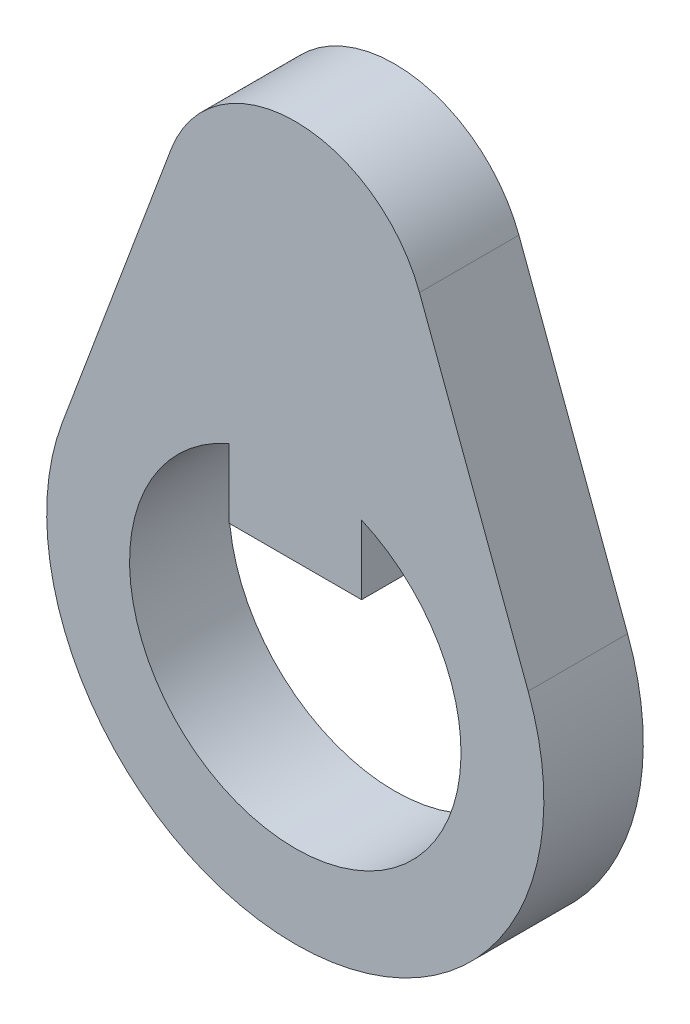
SolidWorks part; units mm, degrees
ref_plane "Front Plane" through (0, 0, 0) normal (0, 0, 1) x (1, 0, 0)
ref_plane "Top Plane" through (0, 0, 0) normal (0, 1, 0) x (1, 0, 0)
ref_plane "Right Plane" through (0, 0, 0) normal (1, 0, 0) x (0, 0, -1)
sketch "Sketch1" plane through (0, 0, 0) normal (0, 0, 1) x (1, 0, 0)
  line L0 (4, 15) -> (-4, 15)
  line L1 (4, 15) -> (4, 5)
  line L2 (4, 5) -> (-4, 5)
  line L3 (-4, 15) -> (-4, 5)
  line L4 (4, 15) -> (-4, 5) construction
  line L5 (4, 5) -> (-4, 15) construction
  line L6 (-7.494, 22.8) -> (-14.0512, 5.25)
  line L7 (7.494, 22.8) -> (14.0512, 5.25)
  circle A1 centre (0, 0) radius 10
  arc A2 (-7.494, 22.8) -> (7.494, 22.8) centre (0, 20) cw
  arc A3 (-14.0512, 5.25) -> (14.0512, 5.25) centre (0, 0) ccw
  point P3 (0, 10)
  dimension "D4" = 20
  dimension "D5" = 15
  dimension "D6" = 8
  dimension "D1" = 20
  dimension "D2" = 8
  dimension "D3" = 10
extrude "Boss-Extrude1" add sketch "Sketch1" along normal blind 6 contours L6 A3 L7 A2 A1 L3 L0 L1 | A1 L1 L0 L3 | L1 A1 L3 L2
equation "\"shaftDiam\" = 20mm"
equation "\"keyW\" = 8mm"
equation "\"keyL\" = 10mm"
equation "\"clearance\" = 1mm"
equation "\"handleShaftLen\" = 60mm"
equation "\"panelH\" = 80mm"
equation "\"panelW\" = 110mm"
equation "\"D2@Sketch1\"=\"keyW\""
equation "\"D3@Sketch1\"=\"keyL\""
equation "\"D4@Sketch1\"=\"shaftDiam\""
equation "\"D5@Sketch1\"=\"shaftDiam\"*.75"
equation "\"D1@Sketch1\"=\"shaftDiam\""
equation "\"D6@Sketch1\"=\"shaftDiam\"/2.5"
equation "\"D1@Boss-Extrude1\"=\"handleShaftLen\"/10"
